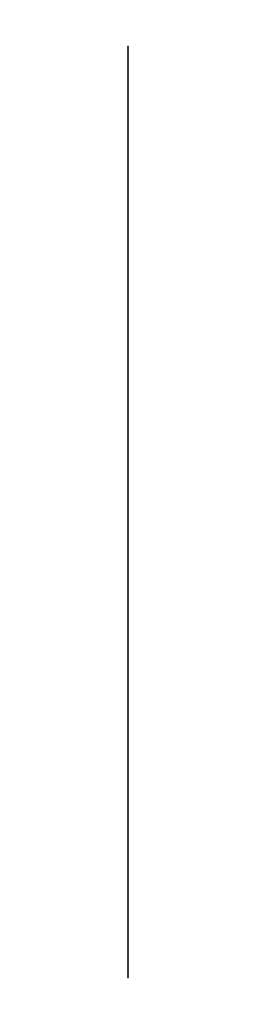
SolidWorks part; units mm, degrees
ref_plane "Front Plane" through (0, 0, 0) normal (0, 0, 1) x (1, 0, 0)
ref_plane "Top Plane" through (0, 0, 0) normal (0, 1, 0) x (1, 0, 0)
ref_plane "Right Plane" through (0, 0, 0) normal (1, 0, 0) x (0, 0, -1)
sketch "草图1" plane through (0, 0, 0) normal (0, 1, 0) x (1, 0, 0)
  circle A0 centre (0, 0) radius 1
extrude "凸台-拉伸1" add sketch "草图1" along normal blind 2000
sketch "草图2" plane through (0, 2000, 0) normal (0, 1, 0) x (1, 0, 0)
  point P0 (0, 0)
sketch "草图3" plane through (0, 0, 0) normal (0, -1, 0) x (1, 0, 0)
  point P0 (0, 0)
